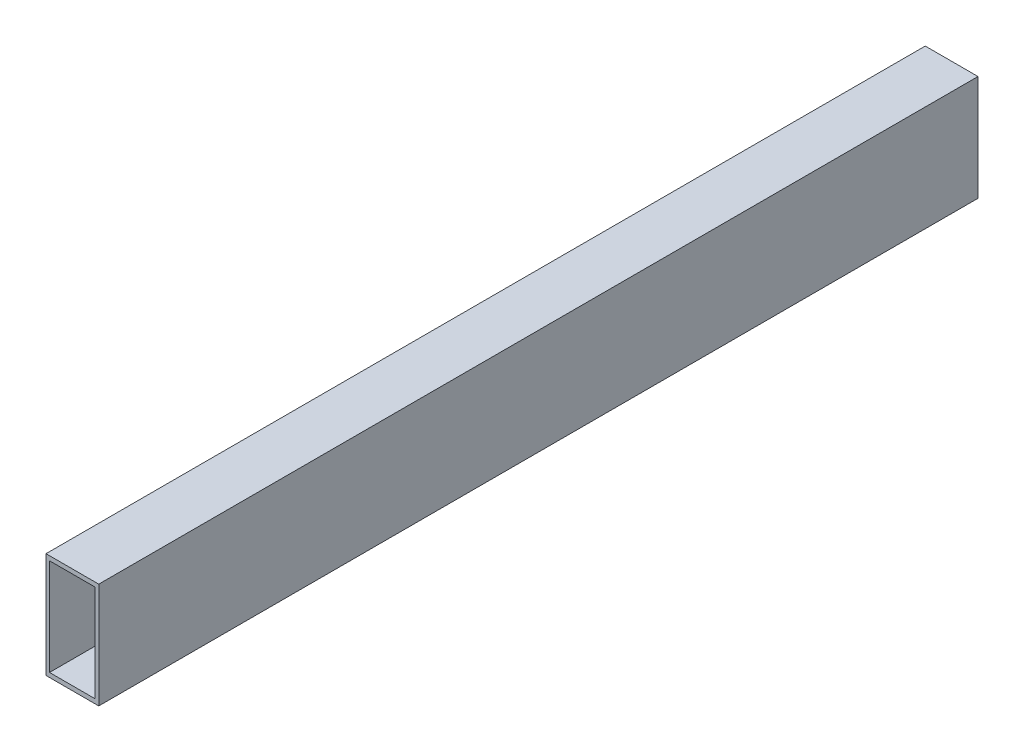
SolidWorks part; units mm, degrees
ref_plane "Front Plane" through (0, 0, 0) normal (0, 0, 1) x (1, 0, 0)
ref_plane "Top Plane" through (0, 0, 0) normal (0, 1, 0) x (1, 0, 0)
ref_plane "Right Plane" through (0, 0, 0) normal (1, 0, 0) x (0, 0, -1)
curve "Curve1"
  spline degree 1 poles (0, 0, -500) (0, 0, 500) knots 0 0 1 1
sketch "Sketch1" plane through (0, 0, 0) normal (0, 0, 1) x (1, 0, 0)
  line L0 (0, 35.3535) -> (0, -33.8384) construction
  line L1 (-30, 60) -> (30, 60)
  line L2 (-30, 60) -> (-30, -60)
  line L3 (-30, -60) -> (30, -60)
  line L4 (30, 60) -> (30, -60)
  line L5 (-26, 55) -> (26, 55)
  line L6 (-26, 55) -> (-26, -55)
  line L7 (-26, -55) -> (26, -55)
  line L8 (26, 55) -> (26, -55)
  line L9 (-39.3939, 0) -> (41.5152, 0) construction
  dimension "D1" = 60
  dimension "D2" = 52
  dimension "D3" = 120
  dimension "D4" = 110
sweep "Sweep1" add profiles "Sketch1" path "Curve1"
